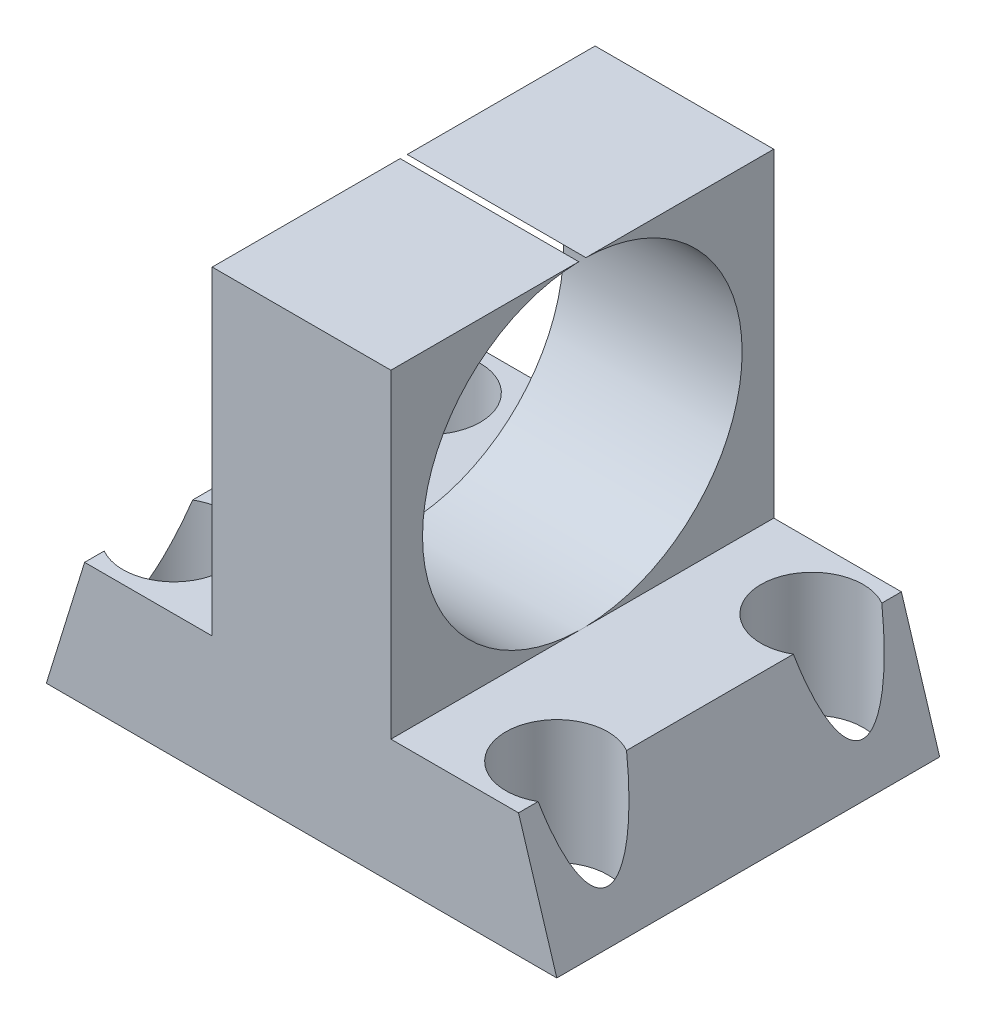
SolidWorks part; units mm, degrees
ref_plane "前视基准面" through (0, 0, 0) normal (0, 0, 1) x (1, 0, 0)
ref_plane "上视基准面" through (0, 0, 0) normal (0, 1, 0) x (1, 0, 0)
ref_plane "右视基准面" through (0, 0, 0) normal (1, 0, 0) x (0, 0, -1)
sketch "草图1" plane through (0, 0, 0) normal (0, 0, 1) x (1, 0, 0)
  line L0 (-10.3686, -4.854) -> (9.6314, -4.854)
  line L1 (9.6314, -4.854) -> (8.1314, 0)
  line L2 (8.1314, 0) -> (3.1314, 0)
  line L3 (3.1314, 0) -> (3.1314, 12.5182)
  line L4 (3.1314, 12.5182) -> (-3.8686, 12.5182)
  line L5 (-3.8686, 12.5182) -> (-3.8686, 0)
  line L6 (-3.8686, 0) -> (-8.8686, 0)
  line L7 (-8.8686, 0) -> (-10.3686, -4.854)
  point P9 (-0.3686, 12.5182)
  point P10 (-0.3686, -4.854)
  point P11 (0, 0)
  dimension "D1" = 20
  dimension "D2" = 5
  dimension "D3" = 5
  dimension "D4" = 7
extrude "凸台-拉伸1" add sketch "草图1" along normal blind 15
sketch "草图2" plane through (3.1314, 0, 0) normal (1, 0, 0) x (0, 0, -1)
  line L0 (0, 0) -> (0, 12.5182) construction
  line L1 (-15, 12.5182) -> (0, 12.5182) construction
  circle A0 centre (-7.5, 6.2591) radius 6.2607
  point P0 (0, 6.2591)
  point P1 (-7.5, 12.5182)
  point P4 (-7.5, 6.2591)
  point P9 (-13.7607, 6.2591)
  point P10 (-1.2393, 6.2591)
  point P11 (0, 0)
  point P12 (0, 0)
  dimension "D1" = 12.5213
extrude "切除-拉伸1" cut sketch "草图2" against normal blind 20
sketch "草图3" plane through (0, -4.854, 0) normal (0, -1, 0) x (1, 0, 0)
  line L0 (-10.3686, 15) -> (9.6314, 15) construction
  line L2 (-10.3686, 15) -> (-10.3686, 0) construction
  line L3 (-0.3686, 0) -> (-0.3686, 15)
  line L4 (-10.3686, 0) -> (9.6314, 0) construction
  line L5 (-10.3686, 7.5) -> (9.6314, 7.5)
  line L6 (9.6314, 15) -> (9.6314, 0) construction
  circle A0 centre (-7.8686, 12.5) radius 2
  circle A1 centre (7.1314, 12.5) radius 2
  circle A2 centre (7.1314, 2.5) radius 2
  circle A3 centre (-7.8686, 2.5) radius 2
  dimension "D1" = 2.5
  dimension "D2" = 2.5
  dimension "D3" = 15
  dimension "D4" = 10
extrude "切除-拉伸2" cut sketch "草图3" against normal blind 20 contours A0 | A1 | A2 | A3
